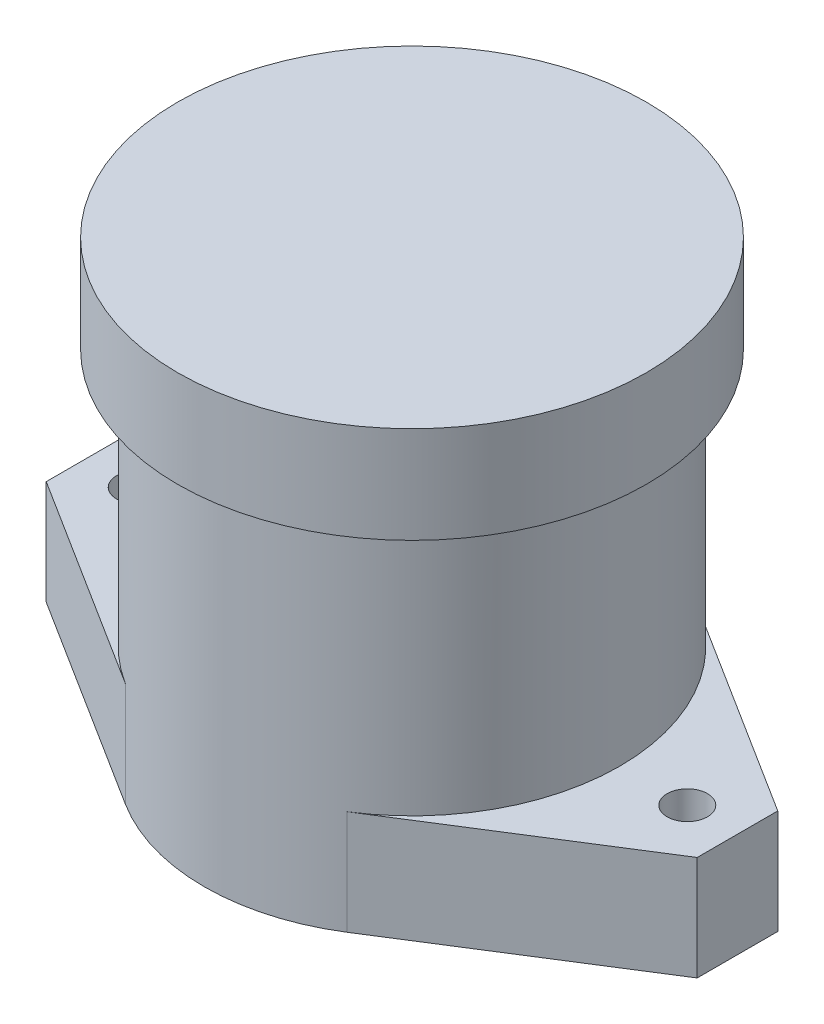
SolidWorks part; units mm, degrees
ref_plane "Front Plane" through (0, 0, 0) normal (0, 0, 1) x (1, 0, 0)
ref_plane "Top Plane" through (0, 0, 0) normal (0, 1, 0) x (1, 0, 0)
ref_plane "Right Plane" through (0, 0, 0) normal (1, 0, 0) x (0, 0, -1)
sketch "Sketch1" plane through (0, 0, 0) normal (0, 1, 0) x (1, 0, 0)
  line L0 (-40.386, -5) -> (-40.386, 5)
  line L1 (-40.386, 5) -> (-13.7584, 21.8029)
  line L2 (13.7584, 21.8029) -> (40.386, 5)
  line L3 (40.386, 5) -> (40.386, -5)
  line L4 (40.386, -5) -> (13.7584, -21.8029)
  line L5 (-13.7584, -21.8029) -> (-40.386, -5)
  line L6 (0, -55) -> (0, 55) construction
  arc A0 (-13.7584, 21.8029) -> (13.7584, 21.8029) centre (0, 0) cw
  arc A1 (13.7584, -21.8029) -> (-13.7584, -21.8029) centre (0, 0) cw
  circle A2 centre (-34.163, 0) radius 2.5
  circle A3 centre (34.163, 0) radius 2.5
  point P2 (40.386, 0)
  point P12 (-40.386, 0)
  point P18 (-34.163, -2.2238)
  point P19 (0, 0)
  dimension "D1" = 5
  dimension "D4" = 51.562
  dimension "D2" = 68.326
  dimension "D3" = 80.772
  dimension "D5" = 10
extrude "Boss-Extrude1" add sketch "Sketch1" along normal blind 12.954
sketch "Sketch2" plane through (0, 12.954, 0) normal (0, 1, 0) x (1, 0, 0)
  arc A0 (13.7584, 21.8029) -> (-13.7584, 21.8029) centre (0, 0) ccw construction
  circle A1 centre (0, 0) radius 25.781
  point P3 (14.2585, 21.4873)
extrude "Boss-Extrude2" add sketch "Sketch2" along normal offset from surface (43.942 mm away) 56.896 up to face at (-34.163, 0, 2.5)
sketch "Sketch3" plane through (0, 56.896, 0) normal (0, 1, 0) x (1, 0, 0)
  circle A0 centre (0, 0) radius 29.083
  dimension "D1" = 58.166
extrude "Boss-Extrude3" add sketch "Sketch3" against normal blind 12
